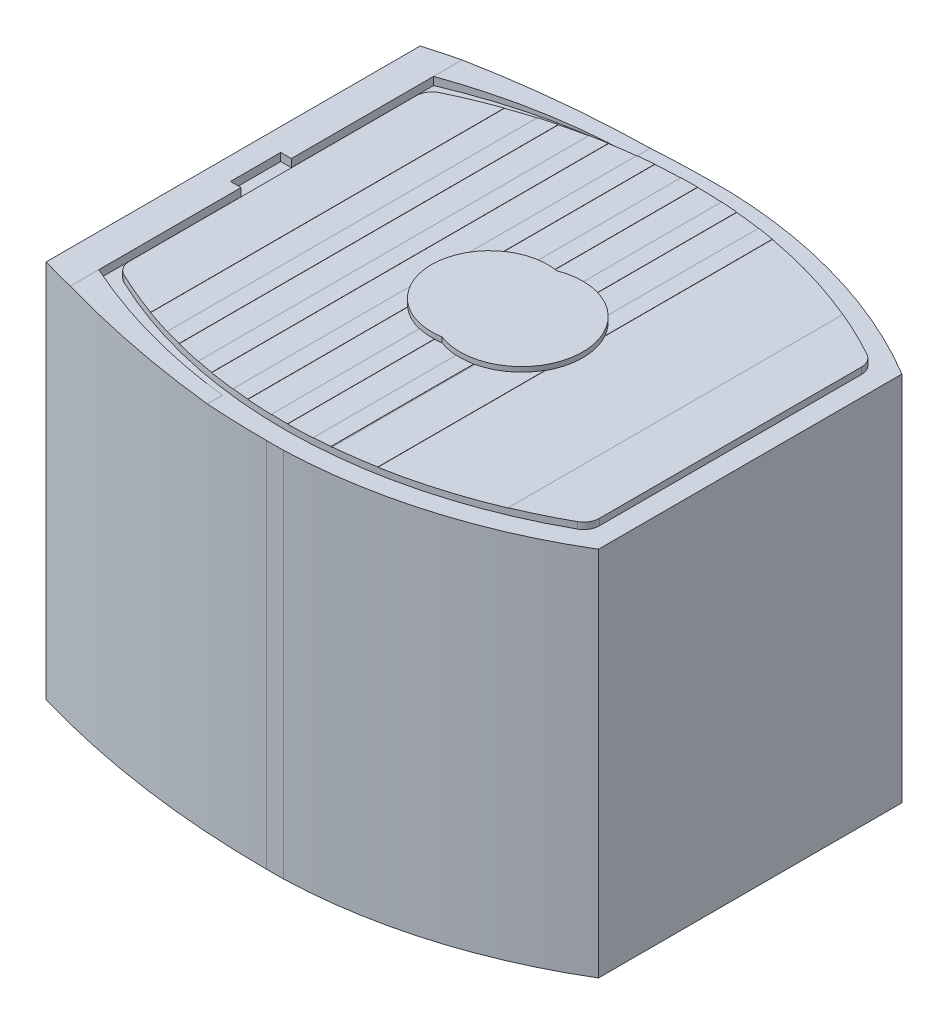
SolidWorks part; units mm, degrees
ref_plane "Front Plane" through (0, 0, 0) normal (0, 0, 1) x (1, 0, 0)
ref_plane "Top Plane" through (0, 0, 0) normal (0, 1, 0) x (1, 0, 0)
ref_plane "Right Plane" through (0, 0, 0) normal (1, 0, 0) x (0, 0, -1)
ref_plane "Plane1" through (0, -30.0219, 0) normal (0, -1, 0) x (-1, 0, 0)
sketch "Sketch1" plane through (0, -30.0219, 0) normal (0, -1, 0) x (-1, 0, 0)
  line L0 (-83.1596, 21.6514) -> (-84.7621, 21.6514)
  line L1 (-108.1278, 14.7553) -> (-108.1278, -14.3785)
  line L2 (-84.7621, -21.2746) -> (-83.1596, -21.2746)
  line L3 (-58.4708, -17.7694) -> (-58.4708, 18.1462)
  arc A0 (-58.4708, 18.1462) -> (-83.1596, 21.6514) centre (-83.1159, -66.7406) ccw
  arc A1 (-84.7621, 21.6514) -> (-108.1278, 14.7553) centre (-83.1596, -26.8108) ccw
  arc A2 (-108.1278, -14.3785) -> (-84.7621, -21.2746) centre (-83.1596, 27.1875) ccw
  arc A3 (-83.1596, -21.2746) -> (-58.4708, -17.7694) centre (-83.1159, 67.1173) ccw
extrude "Boss-Extrude1" add sketch "Sketch1" against normal blind 40
ref_plane "Plane2" through (0, 0, 0) normal (0, 0, 1) x (1, 0, 0)
sketch "Sketch2" plane through (0, 0, 0) normal (0, 0, 1) x (1, 0, 0)
  line L0 (54.8208, 15.1185) -> (54.8208, 6.4017)
  line L1 (54.8208, 6.4017) -> (61.6458, 6.4017)
  line L2 (61.6458, 6.4017) -> (77.2668, 5.6397)
  line L3 (77.2668, 5.6397) -> (110.4482, 5.6397)
  line L4 (110.4482, 5.6397) -> (110.4482, 15.1185)
  line L5 (110.4482, 15.1185) -> (54.8208, 15.1185)
extrude "Cut-Extrude1" cut sketch "Sketch2" against normal blind 40 and the other way blind 40
ref_plane "Plane3" through (0, 5.6397, 0) normal (0, 1, 0) x (1, 0, 0)
sketch "Sketch3" plane through (0, 5.6397, 0) normal (0, 1, 0) x (1, 0, 0)
  line L0 (60.6298, -2.2246) -> (61.6458, -2.2246)
  line L1 (61.6458, -2.2246) -> (61.6458, -15.8898)
  line L2 (77.2668, -19.6236) -> (77.2668, -24.4849)
  line L3 (77.2668, -24.4849) -> (116.1455, -24.4849)
  line L4 (116.1455, -24.4849) -> (116.1455, 24.1419)
  line L5 (116.1455, 24.1419) -> (77.2668, 24.1419)
  line L6 (77.2668, 24.1419) -> (77.2668, 20.0004)
  line L7 (61.6458, 16.2666) -> (61.6458, 2.6014)
  line L8 (61.6458, 2.6014) -> (60.6298, 2.6014)
  line L9 (60.6298, 2.6014) -> (60.6298, -2.2246)
  arc A0 (61.6458, -15.8898) -> (77.2668, -19.6236) centre (80.5192, 28.5266) ccw
  arc A1 (77.2668, 20.0004) -> (61.6458, 16.2666) centre (80.5192, -28.1499) ccw
extrude "Cut-Extrude2" cut sketch "Sketch3" along normal blind 40
ref_plane "Plane4" through (0, 5.6397, 0) normal (0, 1, 0) x (1, 0, 0)
sketch "Sketch4" plane through (0, 5.6397, 0) normal (0, 1, 0) x (1, 0, 0)
  line L0 (62.2808, 13.9716) -> (62.2808, -13.595)
  line L1 (106.2228, -12.3857) -> (106.2228, 12.7623)
  arc A0 (62.2808, -13.595) -> (63.1464, -14.9695) centre (63.8048, -13.595) ccw
  arc A1 (63.1464, -14.9695) -> (105.4373, -13.7189) centre (83.0798, 26.6428) ccw
  arc A2 (105.4373, -13.7189) -> (106.2228, -12.3857) centre (104.6988, -12.3857) ccw
  arc A3 (106.2228, 12.7623) -> (105.4371, 14.0956) centre (104.6988, 12.7623) ccw
  arc A4 (105.4371, 14.0956) -> (63.1466, 15.3461) centre (83.0794, -26.2792) ccw
  arc A5 (63.1466, 15.3461) -> (62.2808, 13.9716) centre (63.8048, 13.9716) ccw
extrude "Boss-Extrude2" add sketch "Sketch4" along normal blind 0.6223
ref_plane "Plane5" through (0, 6.2366, 0) normal (0, 1, 0) x (1, 0, 0)
sketch "Sketch5" plane through (0, 6.2366, 0) normal (0, 1, 0) x (1, 0, 0)
  line L0 (60.8798, -1.9746) -> (61.8958, -1.9746)
  line L1 (61.8958, -1.9746) -> (61.8958, -15.7241)
  line L2 (61.8958, -15.7241) -> (70.7252, -18.2616)
  line L3 (70.7252, -18.2616) -> (77.5168, -19.3894)
  line L4 (77.5168, -19.3894) -> (77.5168, -26.2792)
  line L5 (77.5168, -26.2792) -> (112.5986, -26.2792)
  line L6 (112.5986, -26.2792) -> (112.5986, 26.6428)
  line L7 (112.5986, 26.6428) -> (77.5168, 26.6428)
  line L8 (77.5168, 26.6428) -> (77.5168, 19.7661)
  line L9 (77.5168, 19.7661) -> (68.798, 18.2088)
  line L10 (68.798, 18.2088) -> (61.8958, 16.1008)
  line L11 (61.8958, 16.1008) -> (61.8958, 2.3514)
  line L12 (61.8958, 2.3514) -> (60.8798, 2.3514)
  line L13 (60.8798, 2.3514) -> (60.8798, -1.9746)
  line L14 (106.2228, -12.3857) -> (106.2228, 12.7623)
  line L15 (100.965, 16.266) -> (100.965, -15.89)
  line L16 (87.4776, -5.5567) -> (87.4776, -19.2874)
  line L17 (91.313, -18.7569) -> (91.313, 19.1322)
  line L18 (89.7382, 19.3897) -> (89.7382, 4.8707)
  line L19 (89.7382, 4.8707) -> (87.4776, -5.5567)
  line L20 (87.3506, -19.2994) -> (87.3506, 19.6745)
  line L21 (85.7758, 19.7937) -> (85.7758, -19.4186)
  line L22 (83.3882, -19.4964) -> (83.3882, 19.8715)
  line L23 (81.8134, 19.8552) -> (81.8134, -19.4801)
  line L24 (79.4258, -19.3525) -> (79.4258, 19.7277)
  line L25 (77.851, 19.5755) -> (77.851, -19.2002)
  line L26 (73.8886, 18.9482) -> (73.8886, -18.5727)
  line L27 (75.4634, -18.8645) -> (75.4634, 19.2398)
  line L28 (69.9262, 17.9586) -> (69.9262, -17.5828)
  line L29 (71.501, -18.021) -> (71.501, 18.3966)
  line L30 (67.5386, -16.8013) -> (67.5386, 17.1773)
  line L31 (62.2808, 13.9716) -> (62.2808, -13.595)
  arc A0 (100.965, -15.89) -> (105.4373, -13.7189) centre (83.0798, 26.6428) ccw
  arc A1 (105.4373, -13.7189) -> (106.2228, -12.3857) centre (104.6988, -12.3857) ccw
  arc A2 (106.2228, 12.7623) -> (105.4371, 14.0956) centre (104.6988, 12.7623) ccw
  arc A3 (105.4371, 14.0956) -> (100.965, 16.266) centre (83.0794, -26.2792) ccw
  arc A4 (87.4776, -19.2874) -> (91.313, -18.7569) centre (83.0798, 26.6428) ccw
  arc A5 (91.313, 19.1322) -> (89.7382, 19.3897) centre (83.0794, -26.2792) ccw
  arc A6 (85.7758, -19.4186) -> (87.3506, -19.2994) centre (83.0798, 26.6428) ccw
  arc A7 (87.3506, 19.6745) -> (85.7758, 19.7937) centre (83.0794, -26.2792) ccw
  arc A8 (81.8134, -19.4801) -> (83.3882, -19.4964) centre (83.0798, 26.6428) ccw
  arc A9 (83.3882, 19.8715) -> (81.8134, 19.8552) centre (83.0794, -26.2792) ccw
  arc A10 (77.851, -19.2002) -> (79.4258, -19.3525) centre (83.0798, 26.6428) ccw
  arc A11 (79.4258, 19.7277) -> (77.851, 19.5755) centre (83.0794, -26.2792) ccw
  arc A12 (73.8886, -18.5727) -> (75.4634, -18.8645) centre (83.0798, 26.6428) ccw
  arc A13 (75.4634, 19.2398) -> (73.8886, 18.9482) centre (83.0794, -26.2792) ccw
  arc A14 (69.9262, -17.5828) -> (71.501, -18.021) centre (83.0798, 26.6428) ccw
  arc A15 (71.501, 18.3966) -> (69.9262, 17.9586) centre (83.0794, -26.2792) ccw
  arc A16 (62.2808, -13.595) -> (63.1464, -14.9695) centre (63.8048, -13.595) ccw
  arc A17 (63.1464, -14.9695) -> (67.5386, -16.8013) centre (83.0798, 26.6428) ccw
  arc A18 (67.5386, 17.1773) -> (63.1466, 15.3461) centre (83.0794, -26.2792) ccw
  arc A19 (63.1466, 15.3461) -> (62.2808, 13.9716) centre (63.8048, 13.9716) ccw
extrude "Cut-Extrude3" cut sketch "Sketch5" along normal blind 0.0254
ref_plane "Plane6" through (0, -30.0219, 0) normal (0, -1, 0) x (-1, 0, 0)
sketch "Sketch6" plane through (0, -30.0219, 0) normal (0, -1, 0) x (-1, 0, 0)
  line L0 (-103.354, 3.2207) -> (-102.1966, 2.3)
  line L1 (-102.1966, 2.3) -> (-103.5528, 1.7103)
  line L2 (-103.5528, 1.7103) -> (-102.3196, 0.894)
  line L3 (-102.3196, 0.894) -> (-103.6193, 0.1884)
  line L4 (-103.6193, 0.1884) -> (-102.3196, -0.5173)
  line L5 (-102.3196, -0.5173) -> (-103.5528, -1.3336)
  line L6 (-103.5528, -1.3336) -> (-102.1966, -1.9233)
  line L7 (-102.1966, -1.9233) -> (-103.354, -2.844)
  arc A0 (-103.354, -2.844) -> (-103.354, 3.2207) centre (-86.1568, 0.1884) ccw
extrude "Cut-Extrude4" cut sketch "Sketch6" against normal blind 2.032
ref_plane "Plane7" through (0, 6.262, 0) normal (0, 1, 0) x (1, 0, 0)
sketch "Sketch7" plane through (0, 6.262, 0) normal (0, 1, 0) x (1, 0, 0)
  arc A0 (84.0546, -5.319) -> (84.0546, 5.6957) centre (86.1568, 0.1884) ccw
  arc A1 (84.0546, 5.6957) -> (84.0546, -5.319) centre (83.1088, 0.1884) ccw
extrude "Boss-Extrude3" add sketch "Sketch7" against normal blind 0.464 and the other way blind 0.464
